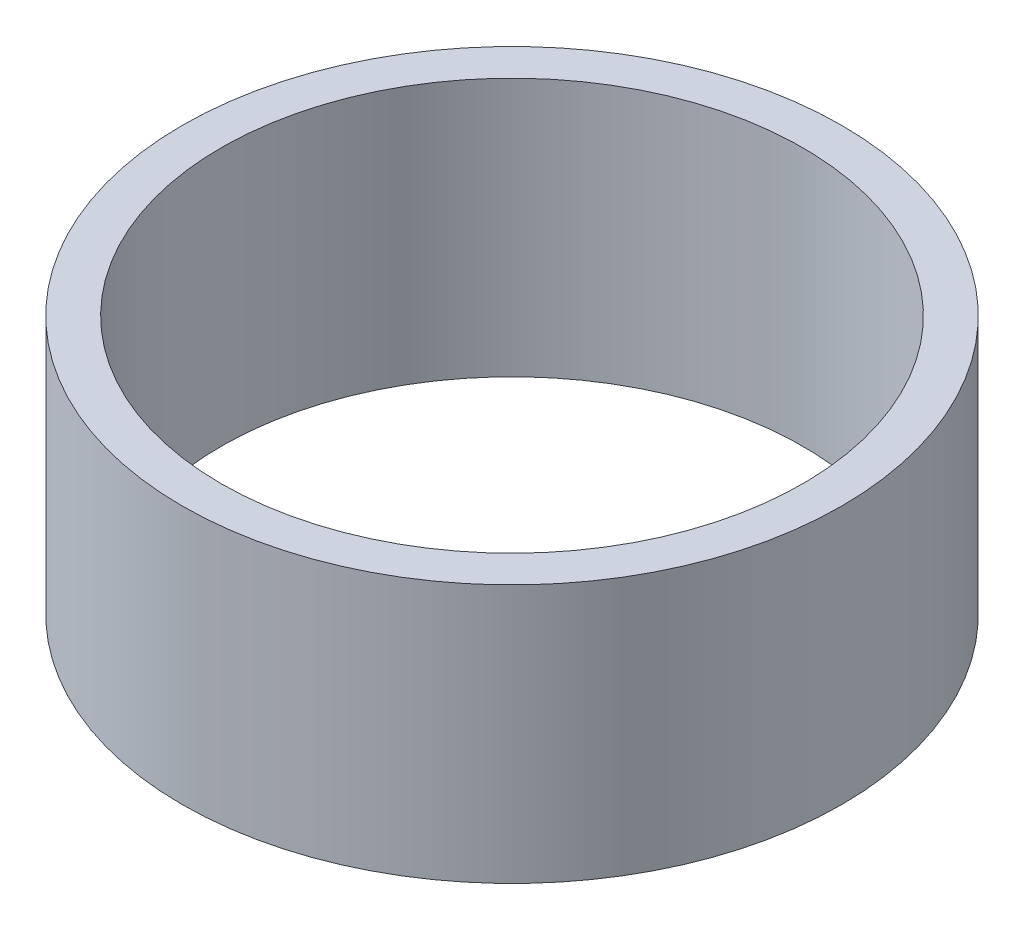
SolidWorks part; units mm, degrees
material "橡胶"
ref_plane "前视基准面" through (0, 0, 0) normal (0, 0, 1) x (1, 0, 0)
ref_plane "上视基准面" through (0, 0, 0) normal (0, 1, 0) x (1, 0, 0)
ref_plane "右视基准面" through (0, 0, 0) normal (1, 0, 0) x (0, 0, -1)
sketch "草图1" plane through (0, 0, 0) normal (0, 1, 0) x (1, 0, 0)
  circle A0 centre (0, 0) radius 22.5
  dimension "D1" = 45
extrude "拉伸-薄壁1" add sketch "草图1" along normal blind 20 thin
